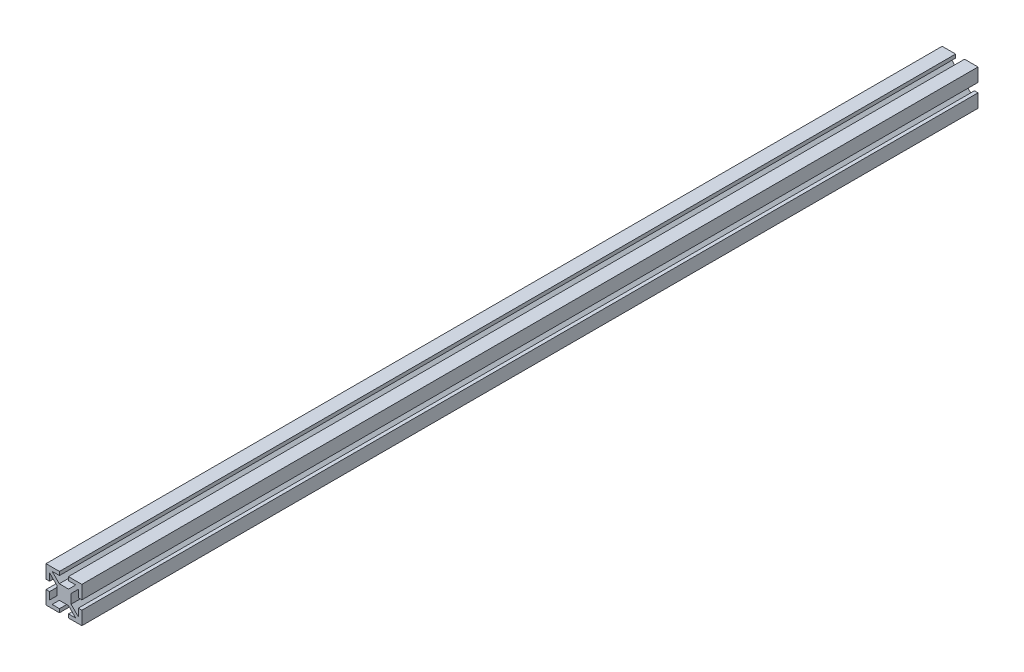
SolidWorks part; units mm, degrees
ref_plane "Front Plane" through (0, 0, 0) normal (0, 0, 1) x (1, 0, 0)
ref_plane "Top Plane" through (0, 0, 0) normal (0, 1, 0) x (1, 0, 0)
ref_plane "Right Plane" through (0, 0, 0) normal (1, 0, 0) x (0, 0, -1)
sketch "Sketch1" plane through (0, 0, 0) normal (0, 0, 1) x (1, 0, 0)
  line L0 (0, 4) -> (0, -4) construction
  line L1 (-2.5858, 4) -> (2.5858, 4)
  line L2 (-4, 2.5858) -> (-4, -2.5858)
  line L5 (-10, 10) -> (0, 0) construction
  line L6 (0, 10) -> (0, 4) construction
  line L7 (-4, 2.5858) -> (-8, 6.5858)
  line L8 (-6.5858, 8) -> (-2.5, 8)
  line L9 (-2.5, 8) -> (-2.5, 10)
  line L10 (-2.5, 10) -> (-10, 10)
  line L11 (-10, 10) -> (-10, 2.5)
  line L12 (-10, 2.5) -> (-8, 2.5)
  line L13 (-8, 2.5) -> (-8, 6.5858)
  line L14 (-4, 0) -> (4, 0) construction
  line L15 (-4, 0) -> (-10, 0) construction
  line L16 (-2.5858, 4) -> (-6.5858, 8)
  line L17 (-10, -10) -> (0, 0) construction
  line L18 (-2.5858, -4) -> (-6.5858, -8)
  line L19 (-8, -2.5) -> (-8, -6.5858)
  line L20 (-10, -2.5) -> (-8, -2.5)
  line L21 (-10, -10) -> (-10, -2.5)
  line L22 (-2.5, -10) -> (-10, -10)
  line L23 (-2.5, -8) -> (-2.5, -10)
  line L24 (-6.5858, -8) -> (-2.5, -8)
  line L25 (-4, -2.5858) -> (-8, -6.5858)
  line L26 (-2.5858, -4) -> (2.5858, -4)
  line L27 (10, -10) -> (0, 0) construction
  line L28 (4, 0) -> (10, 0) construction
  line L29 (10, 10) -> (0, 0) construction
  line L30 (4, -2.5858) -> (8, -6.5858)
  line L31 (6.5858, -8) -> (2.5, -8)
  line L32 (2.5, -8) -> (2.5, -10)
  line L33 (2.5, -10) -> (10, -10)
  line L34 (10, -10) -> (10, -2.5)
  line L35 (10, -2.5) -> (8, -2.5)
  line L36 (8, -2.5) -> (8, -6.5858)
  line L37 (2.5858, -4) -> (6.5858, -8)
  line L38 (2.5858, 4) -> (6.5858, 8)
  line L39 (8, 2.5) -> (8, 6.5858)
  line L40 (10, 2.5) -> (8, 2.5)
  line L41 (10, 10) -> (10, 2.5)
  line L42 (2.5, 10) -> (10, 10)
  line L43 (2.5, 8) -> (2.5, 10)
  line L44 (6.5858, 8) -> (2.5, 8)
  line L45 (4, 2.5858) -> (8, 6.5858)
  line L46 (4, 2.5858) -> (4, -2.5858)
  point P0 (0, 0)
  dimension "D1" = 10
  dimension "D2" = 4
  dimension "D3" = 2
  dimension "D4" = 10
  dimension "D5" = 2
  dimension "D6" = 2.5
  dimension "D7" = 2.5
  dimension "D8" = 4
  dimension "D9" = 1
  dimension "D10" = 1
extrude "Boss-Extrude1" add sketch "Sketch1" along normal mid plane 500
sketch "Sketch2" plane through (4, 0, 0) normal (1, 0, 0) x (0, 0, -1)
  line L0 (-250, -2.5858) -> (-250, 2.5858) construction
  circle A0 centre (-240, 0) radius 2.5
  circle A1 centre (-90, 0) radius 2.5
  dimension "D1" = 5
  dimension "D2" = 5
  dimension "D3" = 10
  dimension "D4" = 160
extrude "Cut-Extrude1" cut sketch "Sketch2" against normal blind 10
